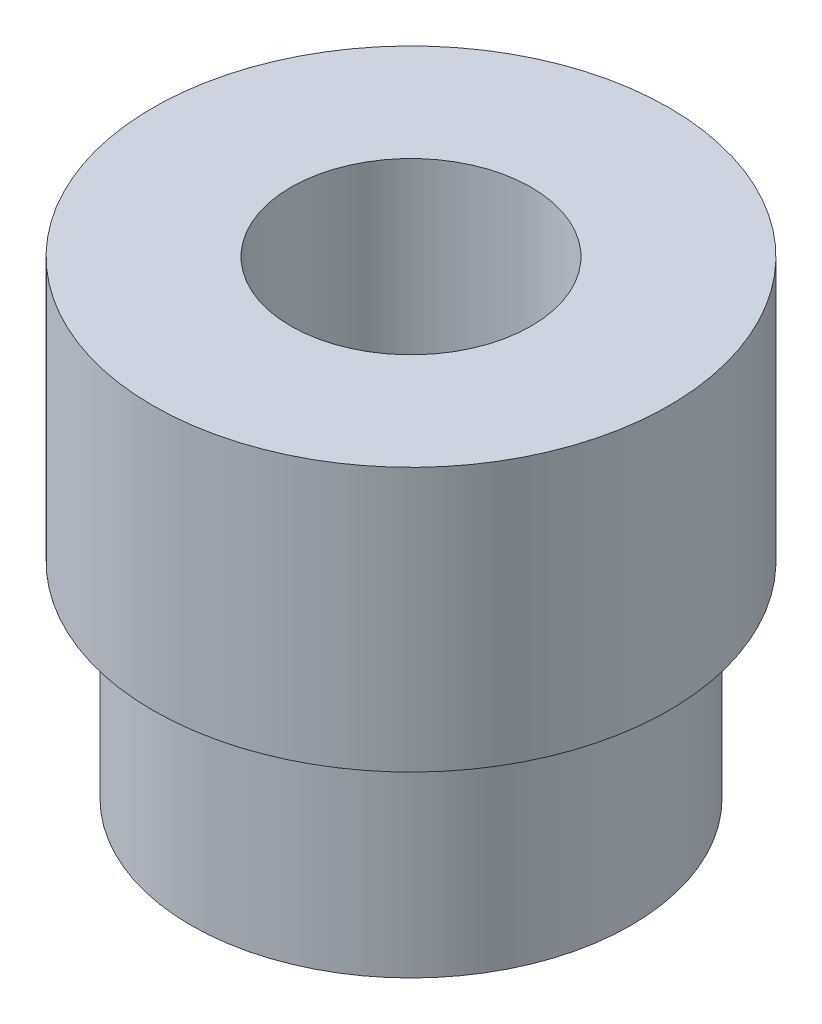
SolidWorks part; units mm, degrees
ref_plane "Front Plane" through (0, 0, 0) normal (0, 0, 1) x (1, 0, 0)
ref_plane "Top Plane" through (0, 0, 0) normal (0, 1, 0) x (1, 0, 0)
ref_plane "Right Plane" through (0, 0, 0) normal (1, 0, 0) x (0, 0, -1)
sketch "Sketch1" plane through (0, 0, 0) normal (0, 1, 0) x (1, 0, 0)
  circle A0 centre (0, 0) radius 2.4
  circle A1 centre (0, 0) radius 7.3
  dimension "D1" = 14.6
  dimension "D2" = 4.8
extrude "Boss-Extrude1" add sketch "Sketch1" along normal blind 10
sketch "Sketch2" plane through (0, 10, 0) normal (0, 1, 0) x (1, 0, 0)
  circle A0 centre (0, 0) radius 7.3 construction
  circle A1 centre (0, 0) radius 7.3
  circle A2 centre (0, 0) radius 8.8
  dimension "D1" = 1.5
extrude "Boss-Extrude2" add sketch "Sketch2" against normal blind 3
sketch "Sketch3" plane through (0, 10, 0) normal (0, 1, 0) x (1, 0, 0)
  circle A0 centre (0, 0) radius 2.4 construction
  circle A1 centre (0, 0) radius 8.8
  circle A2 centre (0, 0) radius 8.8
  circle A3 centre (0, 0) radius 2.4
  dimension "D1" = 0
extrude "Boss-Extrude3" add sketch "Sketch3" along normal blind 6
sketch "Sketch4" plane through (0, 16, 0) normal (0, 1, 0) x (1, 0, 0)
  circle A0 centre (0, 0) radius 2.4 construction
  circle A1 centre (0, 0) radius 2.4
  circle A2 centre (0, 0) radius 0.9
  circle A3 centre (0, 0) radius 4.2
  circle M2 centre (0, 0) radius 2.4
  dimension "D2" = 8.4
  dimension "D1" = 1.5
extrude "Cut-Extrude1" cut sketch "Sketch4" against normal blind 43 contours A3 M2
sketch "Sketch5" plane through (0, 0, 0) normal (0, -1, 0) x (1, 0, 0)
  circle A0 centre (0, 0) radius 7.3 construction
  circle A1 centre (0, 0) radius 7.3
  circle A2 centre (0, 0) radius 7.5
  dimension "D1" = 0.2
extrude "Boss-Extrude4" add sketch "Sketch5" against normal up to next
sketch "Sketch6" plane through (0, 0, 0) normal (0, -1, 0) x (1, 0, 0)
  circle A0 centre (0, 0) radius 4.2 construction
  circle A1 centre (0, 0) radius 4.2
  circle A2 centre (0, 0) radius 4.1
  dimension "D1" = 0.1
extrude "Boss-Extrude5" add sketch "Sketch6" against normal up to surface (16 mm away) up to face at (0, 16, 4.2)
